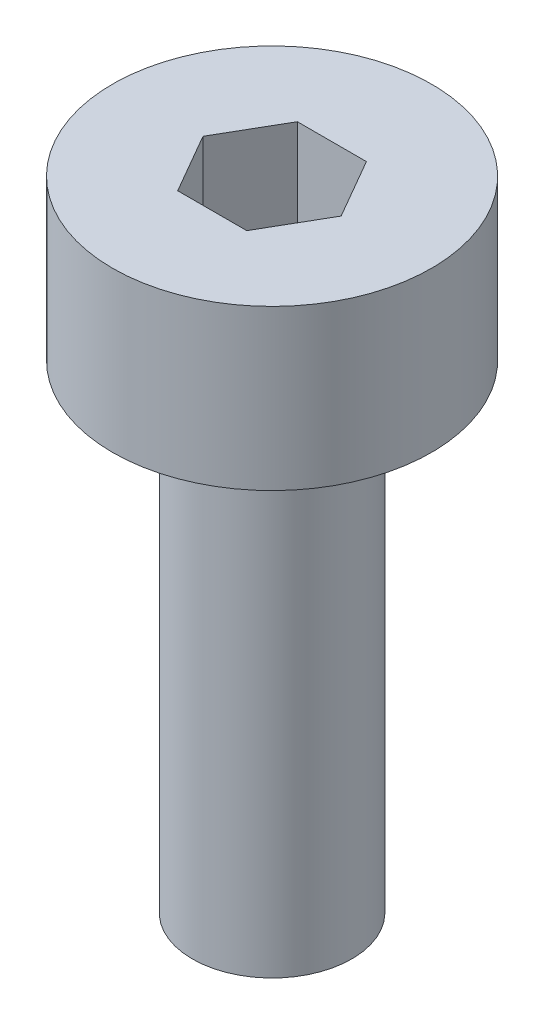
SolidWorks part; units mm, degrees
ref_plane "Front Plane" through (0, 0, 0) normal (0, 0, 1) x (1, 0, 0)
ref_plane "Top Plane" through (0, 0, 0) normal (0, 1, 0) x (1, 0, 0)
ref_plane "Right Plane" through (0, 0, 0) normal (1, 0, 0) x (0, 0, -1)
sketch "Sketch1" plane through (0, 0, 0) normal (0, 1, 0) x (1, 0, 0)
  circle A0 centre (0, 0) radius 2
  dimension "D1" = 4
extrude "Boss-Extrude1" add sketch "Sketch1" along normal blind 12
sketch "Sketch2" plane through (0, 12, 0) normal (0, 1, 0) x (1, 0, 0)
  circle A0 centre (0, 0) radius 4
  dimension "D1" = 8
extrude "Boss-Extrude2" add sketch "Sketch2" along normal blind 4
sketch "Sketch3" plane through (0, 16, 0) normal (0, 1, 0) x (1, 0, 0)
  line L1 (1.7321, 0) -> (0.866, 1.5)
  line L2 (0.866, 1.5) -> (-0.866, 1.5)
  line L3 (-0.866, 1.5) -> (-1.7321, 0)
  line L4 (-1.7321, 0) -> (-0.866, -1.5)
  line L5 (-0.866, -1.5) -> (0.866, -1.5)
  line L6 (0.866, -1.5) -> (1.7321, 0)
  circle A0 centre (0, 0) radius 1.5 construction
  dimension "D1" = 3
extrude "Cut-Extrude1" cut sketch "Sketch3" against normal blind 2.5
